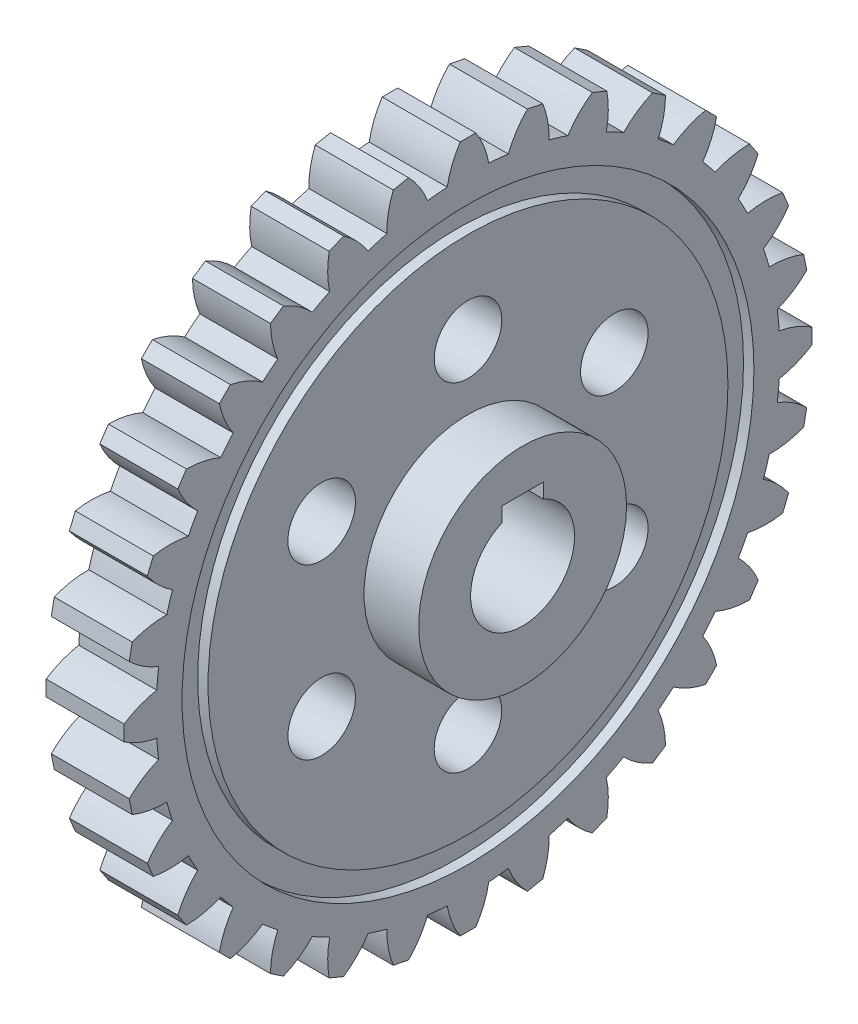
SolidWorks part; units mm, degrees
ref_plane "Front Plane" through (0, 0, 0) normal (0, 0, 1) x (1, 0, 0)
ref_plane "Top Plane" through (0, 0, 0) normal (0, 1, 0) x (1, 0, 0)
ref_plane "Right Plane" through (0, 0, 0) normal (1, 0, 0) x (0, 0, -1)
sketch "Sketch1" plane through (0, 0, 0) normal (1, 0, 0) x (0, 0, -1)
  circle A0 centre (0, 0) radius 60
  dimension "D1" = 120
extrude "Boss-Extrude1" add sketch "Sketch1" along normal mid plane 15
sketch "Sketch2" plane through (7.5, 0, 0) normal (1, 0, 0) x (0, 0, -1)
  line L0 (0, 0) -> (0, 83.7644) construction
  line L1 (-1.5, 66.1365) -> (1.5, 66.1365)
  arc A0 (-4, 59.8665) -> (4, 59.8665) centre (0, 0) cw
  circle A1 centre (0, 0) radius 60 construction
  arc A2 (1.5, 66.1365) -> (4, 59.8665) centre (-12.7267, 56.8306) cw
  arc A3 (-1.5, 66.1365) -> (-4, 59.8665) centre (12.7267, 56.8306) ccw
  point P6 (0, 0)
  dimension "D4" = 17
  dimension "D3" = 4
  dimension "D1" = 3
  dimension "D2" = 6.27
extrude "Boss-Extrude2" add sketch "Sketch2" against normal through all
pattern_circular "CirPattern1" count 32 over 360 about axis through (0, 0, 0) along (1, 0, 0) of "Boss-Extrude2"
sketch "Sketch3" plane through (0, 0, 0) normal (1, 0, 0) x (0, 0, -1)
  circle A0 centre (0, 0) radius 20
  dimension "D1" = 40
extrude "Boss-Extrude3" add sketch "Sketch3" along normal mid plane 36
sketch "Sketch4" plane through (18, 0, 0) normal (1, 0, 0) x (0, 0, -1)
  line L0 (0, 0) -> (0, 25.8375) construction
  line L1 (4, 12) -> (-4, 12)
  line L2 (4, 12) -> (4, 9.1652)
  line L4 (-4, 12) -> (-4, 9.1652)
  line L5 (4, 12) -> (0, 10) construction
  line L6 (0, 10) -> (-4, 12) construction
  arc A0 (-4, 9.1652) -> (4, 9.1652) centre (0, 0) ccw
  point P3 (0, 10)
  dimension "D1" = 10
  dimension "D2" = 8
  dimension "D3" = 12
extrude "Cut-Extrude1" cut sketch "Sketch4" against normal through all
sketch "Sketch5" plane through (7.5, 0, 0) normal (1, 0, 0) x (0, 0, -1)
  circle A0 centre (0, 0) radius 55
  circle A1 centre (0, 0) radius 50
  dimension "D1" = 110
  dimension "D2" = 100
extrude "Cut-Extrude3" cut sketch "Sketch5" against normal blind 2
sketch "Sketch6" plane through (7.5, 0, 0) normal (1, 0, 0) x (0, 0, -1)
  circle A0 centre (0, 32.5) radius 6.5
  dimension "D1" = 13
  dimension "D2" = 32.5
extrude "Cut-Extrude4" cut sketch "Sketch6" against normal through all
pattern_circular "CirPattern2" count 6 over 360 about axis through (0, 0, 0) along (1, 0, 0) of "Cut-Extrude4"
mirror "Mirror1" about plane through (0, 0, 0) normal (1, 0, 0) of "Cut-Extrude3"
